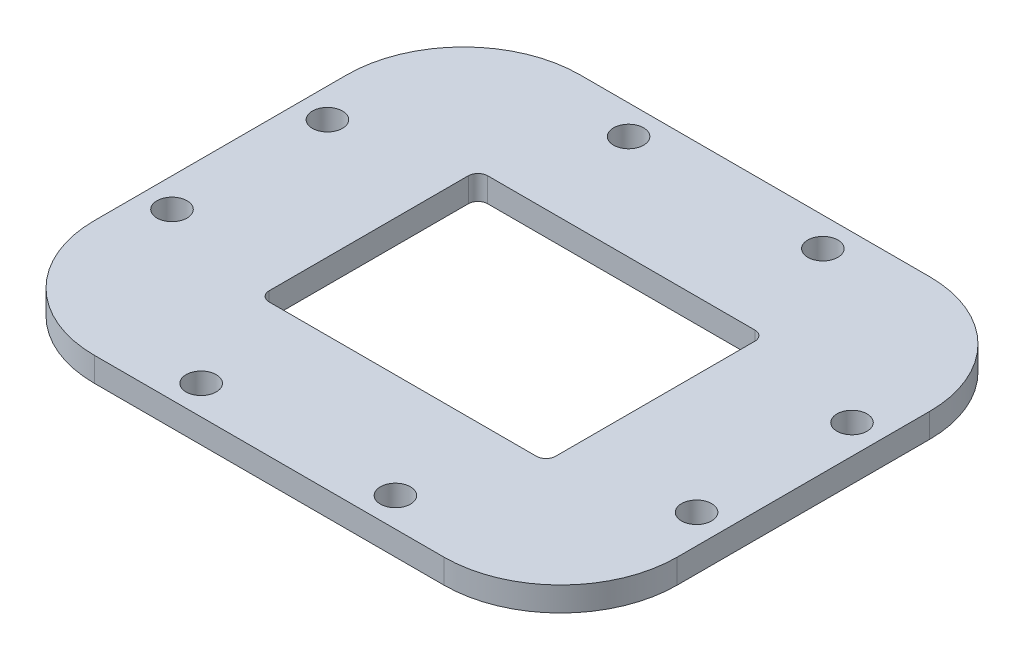
SolidWorks part; units mm, degrees
material "ABS"
ref_plane "前视基准面" through (0, 0, 0) normal (0, 0, 1) x (1, 0, 0)
ref_plane "上视基准面" through (0, 0, 0) normal (0, 1, 0) x (1, 0, 0)
ref_plane "右视基准面" through (0, 0, 0) normal (1, 0, 0) x (0, 0, -1)
other "Configuration Table"
sketch "草图1" plane through (0, 0, 0) normal (0, 1, 0) x (1, 0, 0)
  line L1 (-30, 25) -> (30, 25)
  line L2 (-30, 25) -> (-30, -25)
  line L3 (-30, -25) -> (30, -25)
  line L4 (30, 25) -> (30, -25)
  line L5 (-30, 25) -> (30, -25) construction
  line L6 (-30, -25) -> (30, 25) construction
  line L7 (-14.75, 11.25) -> (14.75, 11.25)
  line L8 (-14.75, 11.25) -> (-14.75, -11.25)
  line L9 (-14.75, -11.25) -> (14.75, -11.25)
  line L10 (14.75, 11.25) -> (14.75, -11.25)
  line L11 (-14.75, 11.25) -> (14.75, -11.25) construction
  line L12 (-14.75, -11.25) -> (14.75, 11.25) construction
  point P0 (0, 0)
  point P6 (0, 0)
  dimension "D1" = 60
  dimension "D2" = 50
  dimension "D3" = 29.5
  dimension "D4" = 22.5
extrude "凸台-拉伸1" add sketch "草图1" along normal blind 2.5
sketch "草图8" plane through (0, 0, 0) normal (0, -1, 0) x (1, 0, 0)
  line L0 (0, 25) -> (0, 0) construction
  line L1 (-30, 25) -> (30, 25) construction
  line L2 (0, 0) -> (30, 0) construction
  line L3 (30, 25) -> (30, -25) construction
  line L4 (-10, 22) -> (10, 22) construction
  circle A0 centre (27, 8) radius 1.55
  circle A1 centre (10, 22) radius 1.55
  circle A2 centre (-10, 22) radius 1.55
  circle A3 centre (-27, 8) radius 1.55
  circle A4 centre (-27, -8) radius 1.55
  circle A5 centre (-10, -22) radius 1.55
  circle A6 centre (10, -22) radius 1.55
  circle A7 centre (27, -8) radius 1.55
  dimension "D1" = 44
  dimension "D2" = 54
  dimension "D3" = 3.1
  dimension "D4" = 20
  dimension "D5" = 16
extrude "切除-拉伸2" cut sketch "草图8" against normal blind 10
fillet "圆角1" radius 1 4 edges at (-14.75, 1.25, 11.25) (14.75, 1.25, 11.25) (14.75, 1.25, -11.25) (-14.75, 1.25, -11.25)
fillet "圆角2" radius 12 4 edges at (30, 1.25, 25) (-30, 1.25, -25) (30, 1.25, -25) (-30, 1.25, 25)
